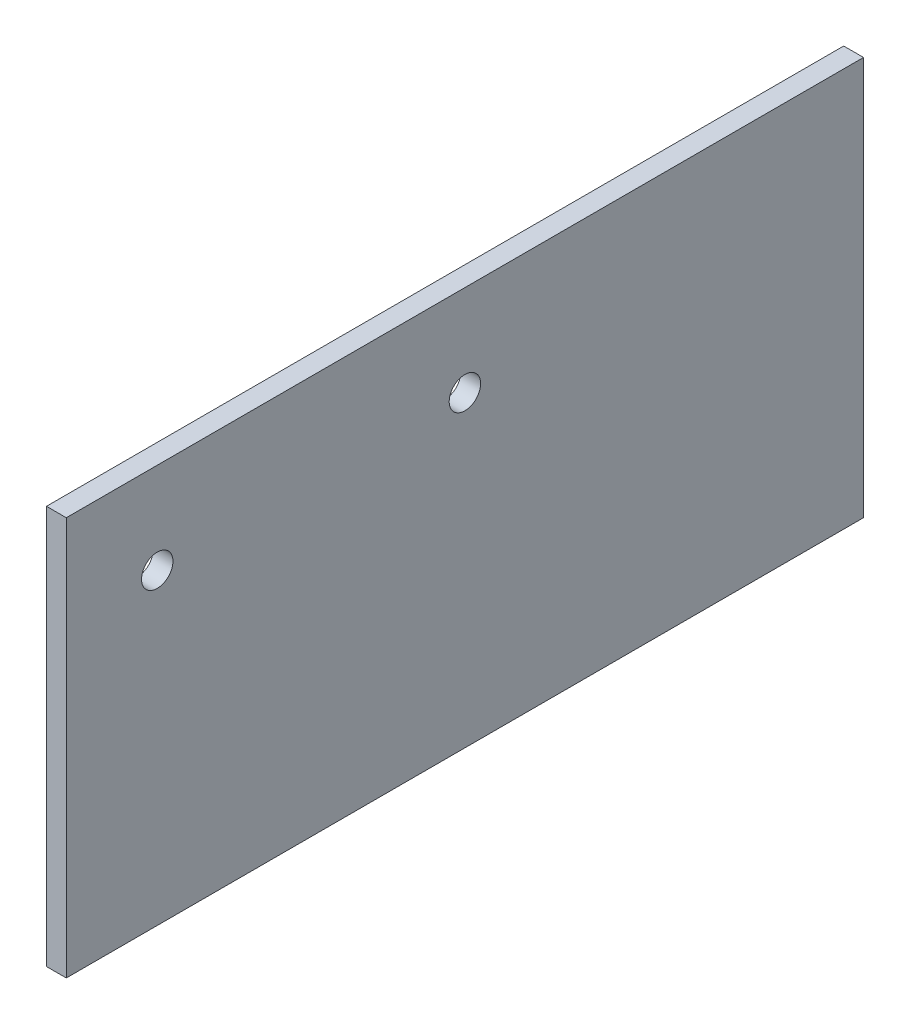
SolidWorks part; units mm, degrees
material "Black Acrylic"
ref_plane "Front Plane" through (0, 0, 0) normal (0, 0, 1) x (1, 0, 0)
ref_plane "Top Plane" through (0, 0, 0) normal (0, 1, 0) x (1, 0, 0)
ref_plane "Right Plane" through (0, 0, 0) normal (1, 0, 0) x (0, 0, -1)
sketch "Sketch1" plane through (0, 0, 0) normal (1, 0, 0) x (0, 0, -1)
  line L1 (-90.5, 90.5) -> (90.5, 90.5)
  line L2 (-90.5, 90.5) -> (-90.5, 0)
  line L3 (-90.5, 0) -> (90.5, 0)
  line L4 (90.5, -90.5) -> (-90.5, 90.5) construction
  line L5 (-90.5, -90.5) -> (90.5, 90.5) construction
  line L6 (90.5, -90.5) -> (90.5, 90.5) construction
  line L7 (90.5, 90.5) -> (90.5, 0)
  point P4 (0, 0)
  dimension "D1" = 181
  dimension "D2" = 181
extrude "Boss-Extrude1" add sketch "Sketch1" along normal mid plane 4.5
extrude "Cut-Extrude1" cut sketch "Sketch2" against normal through all both and the other way through all
sketch "Sketch2" plane through (-88.25, 0, 0) normal (1, 0, 0) x (0, 0, -1)
  line L0 (0, -69.85) -> (0, 69.85) construction
  line L1 (0, 69.85) -> (-69.85, 69.85) construction
  line L2 (69.85, -69.85) -> (0, -69.85) construction
  circle A0 centre (0, -69.85) radius 3.5687
  circle A1 centre (-69.85, 69.85) radius 3.5687
  circle A2 centre (69.85, -69.85) radius 3.5687
  circle A3 centre (0, 69.85) radius 3.5687
